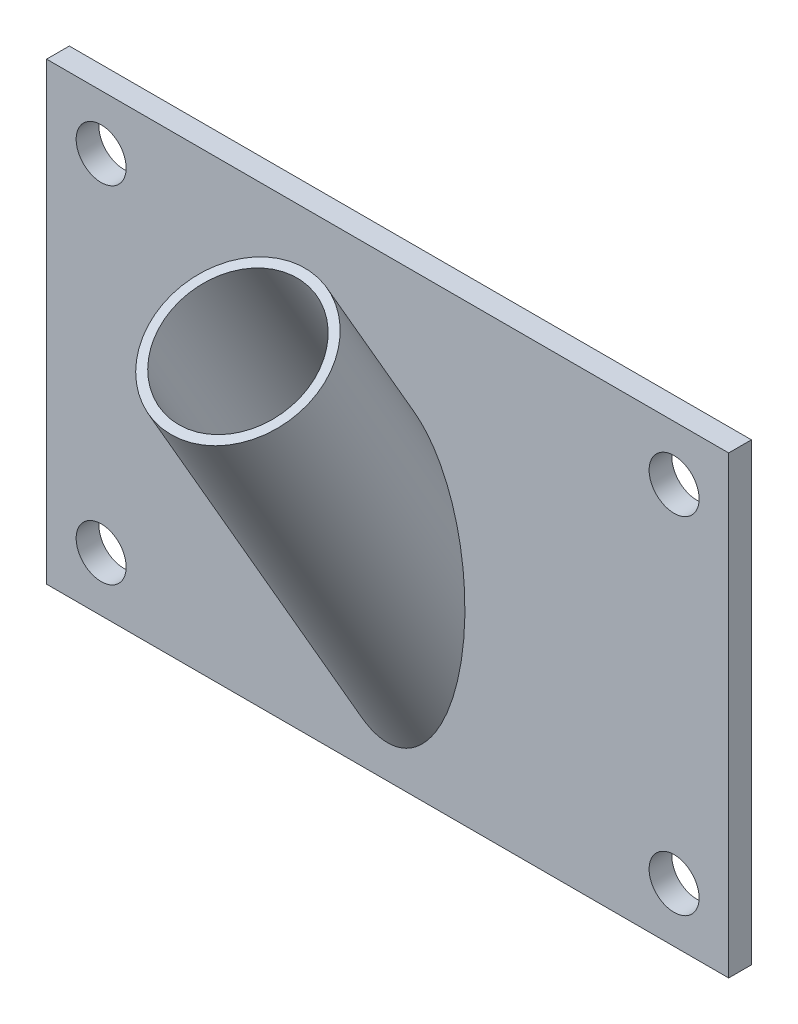
SolidWorks part; units mm, degrees
ref_plane "Płaszczyzna przednia" through (0, 0, 0) normal (0, 0, 1) x (1, 0, 0)
ref_plane "Płaszczyzna górna" through (0, 0, 0) normal (0, 1, 0) x (1, 0, 0)
ref_plane "Płaszczyzna prawa" through (0, 0, 0) normal (1, 0, 0) x (0, 0, -1)
sketch "Szkic1" plane through (0, 0, 0) normal (0, 0, 1) x (1, 0, 0)
  line L0 (55, 0) -> (-55, 0) construction
  line L1 (-75, 50) -> (75, 50)
  line L2 (-75, 50) -> (-75, -50)
  line L3 (-75, -50) -> (75, -50)
  line L4 (75, 50) -> (75, -50)
  line L5 (0, -55) -> (0, 55) construction
  point P4 (-75, 0)
  point P9 (0, -50)
  dimension "D1" = 100
  dimension "150" = 150
  dimension "D2" = 0
extrude "Dodanie-wyciągnięcie1" add sketch "Szkic1" along normal blind 5
hole_wizard "Otwór pod śrubę M101" positions "Szkic2" profile "Szkic3" hole size "M10" standard "ISO" end condition through all
sketch "Szkic2" plane through (0, 0, 5) normal (0, 0, 1) x (1, 0, 0)
  line L0 (-75, 50) -> (-75, -50) construction
  line L2 (75, 50) -> (-75, 50) construction
  point P0 (-63, 38)
  point P9 (-40.8395, 50)
  point P16 (-138.0508, 81.9467)
  dimension "D1" = 12
  dimension "D2" = 12
sketch "Szkic3" plane through (-63, 38, 5) normal (1, 0, 0) x (0, -1, 0)
  line L0 (0, 0) -> (0, 5)
  line L1 (0, 5) -> (5.5, 5)
  line L2 (5.5, 5) -> (5.5, 0)
  line L5 (5.5, 0) -> (0, 0)
  line L11 (0, -6.35) -> (0, 107.95) construction
  dimension "Średnica otworu na wylot" = 11
  dimension "Głębokość otworu na wylot" = 5
mirror "Lustro1" about plane through (0, 0, 0) normal (0, 1, 0) of "Otwór pod śrubę M101" second plane through (0, 0, 0) second plane normal (1, 0, 0)
ref_plane "Płaszczyzna1" through (0, 39.6651, 22.9006) normal (0, 0.866, 0.5) x (-1, 0, 0)
sketch "Szkic4" plane through (0, 39.6651, 22.9006) normal (0, 0.866, 0.5) x (-1, 0, 0)
  line L0 (0, 55) -> (0, -55) construction
  circle A0 centre (0, 8.6831) radius 15
  circle A1 centre (0, 8.6831) radius 17
  dimension "D1" = 30
  dimension "D2" = 2
extrude "Dodanie-wyciągnięcie2" add sketch "Szkic4" along normal blind 15 and the other way up to surface other way up to face at (68.5, -38, 5)
